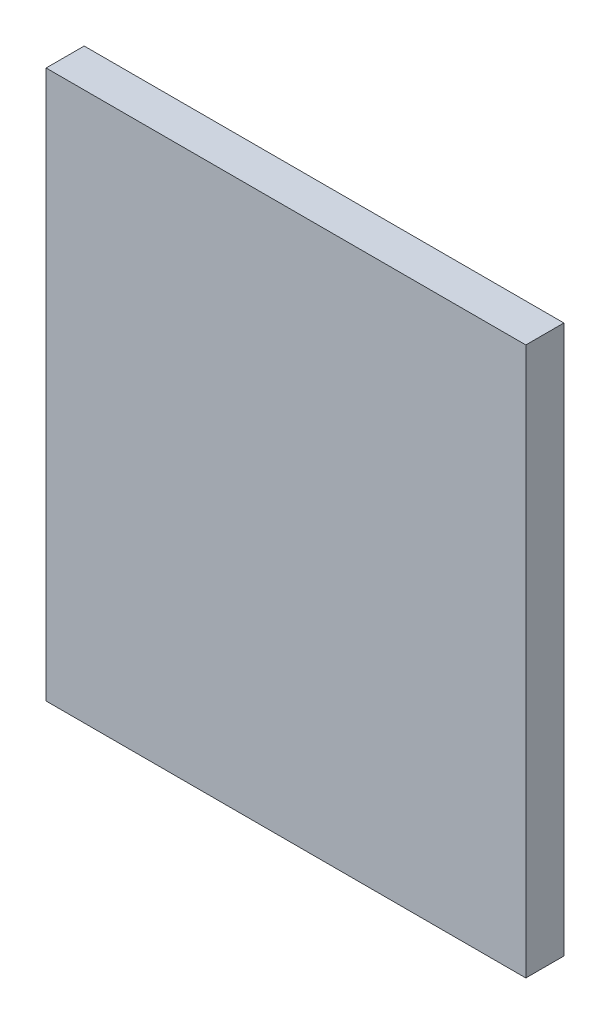
SolidWorks part; units mm, degrees
ref_plane "Front Plane" through (0, 0, 0) normal (0, 0, 1) x (1, 0, 0)
ref_plane "Top Plane" through (0, 0, 0) normal (0, 1, 0) x (1, 0, 0)
ref_plane "Right Plane" through (0, 0, 0) normal (1, 0, 0) x (0, 0, -1)
sketch "Sketch2" [suppressed] plane through (0, 0, 0) normal (0, 0, 1) x (1, 0, 0)
  line L0 (9.8069, 1.0971) -> (9.8069, -3.1704) construction
  line L1 (6.8551, -5.1618) -> (6.8551, -16.1618) construction
  line L2 (6.8551, -16.1618) -> (16.3814, -10.6618) construction
  line L3 (16.3814, -10.6618) -> (6.8551, -5.1618) construction
  line L4 (6.8551, -10.6618) -> (2.6647, -10.6618) construction
  line L5 (9.5069, 1.0971) -> (9.5069, -2.443)
  line L6 (6.5551, -6.3743) -> (6.5551, -9.8618)
  line L7 (8.0551, -15.8154) -> (15.4814, -11.5279)
  line L8 (15.4814, -9.7958) -> (8.0551, -5.5082)
  line L9 (6.0551, -10.3618) -> (3.5127, -10.3618)
  line L10 (10.1069, 1.0971) -> (10.1069, -2.3736)
  line L11 (7.1551, -6.5475) -> (7.1551, -14.7762)
  line L12 (7.9051, -15.2092) -> (15.0314, -11.0948)
  line L13 (15.0314, -10.2288) -> (7.9051, -6.1145)
  line L14 (6.0551, -10.9618) -> (3.5127, -10.9618)
  line L15 (9.5069, 1.0971) -> (9.5069, -3.1704) construction
  line L16 (10.1069, 1.0971) -> (10.1069, -3.1704) construction
  line L17 (6.8551, -10.9618) -> (2.6647, -10.9618) construction
  line L18 (6.8551, -10.3618) -> (2.6647, -10.3618) construction
  line L19 (6.5551, -11.4618) -> (6.5551, -14.9494)
  line L20 (6.5551, -4.6422) -> (6.5551, -16.6814) construction
  line L21 (7.1551, -15.6422) -> (15.7814, -10.6618) construction
  line L22 (15.7814, -10.6618) -> (7.1551, -5.6814) construction
  line L23 (7.1551, -5.6814) -> (7.1551, -15.6422) construction
  line L24 (6.5551, -16.6814) -> (16.9814, -10.6618) construction
  line L25 (16.9814, -10.6618) -> (6.5551, -4.6422) construction
  circle A0 centre (10.1647, -10.6618) radius 7.5 construction
  arc A1 (9.0767, -2.9381) -> (10.5803, -2.8729) centre (10.1647, -10.6618) ccw
  arc A2 (3.0162, -11.5215) -> (3.0162, -9.8021) centre (10.1647, -10.6618) ccw
  arc A3 (9.5069, 1.0971) -> (10.1069, 1.0971) centre (9.8069, 1.0971) cw
  circle A7 centre (10.1647, -10.6618) radius 7.8 construction
  circle A8 centre (10.1647, -10.6618) radius 7.2 construction
  arc A9 (10.1069, -2.3736) -> (10.5803, -2.8729) centre (10.6069, -2.3736) ccw
  arc A10 (9.5069, -2.443) -> (9.0767, -2.9381) centre (9.0069, -2.443) cw
  arc A11 (3.5127, -10.3618) -> (3.0162, -9.8021) centre (3.5127, -9.8618) cw
  arc A12 (3.5127, -10.9618) -> (3.0162, -11.5215) centre (3.5127, -11.4618) ccw
  arc A13 (6.0551, -10.3618) -> (6.5551, -9.8618) centre (6.0551, -9.8618) ccw
  arc A14 (6.5551, -11.4618) -> (6.0551, -10.9618) centre (6.0551, -11.4618) ccw
  arc A15 (15.0314, -11.0948) -> (15.0314, -10.2288) centre (14.7814, -10.6618) ccw
  arc A16 (7.1551, -14.7762) -> (7.9051, -15.2092) centre (7.6551, -14.7762) ccw
  arc A17 (7.1551, -6.5475) -> (7.9051, -6.1145) centre (7.6551, -6.5475) cw
  arc A18 (15.4814, -11.5279) -> (15.4814, -9.7958) centre (14.9814, -10.6618) ccw
  arc A19 (6.5551, -14.9494) -> (8.0551, -15.8154) centre (7.5551, -14.9494) ccw
  arc A20 (6.5551, -6.3743) -> (8.0551, -5.5082) centre (7.5551, -6.3743) cw
  point P1 (0, 0)
  point P9 (0, 0)
  point P10 (0, 0)
  point P11 (-3.6909, -2.988)
  point P12 (6.8551, -10.6618)
  point P13 (-4.1255, -2.8709)
  point P14 (5.6701, -7.3509)
  point P15 (-1.4676, -0.9486)
  point P18 (-9.5501, -9.1992)
  point P72 (0, 0)
  point P73 (0, 0)
  point P74 (0, -9.8504)
  point P75 (0, 0)
  point P76 (0, 0)
  dimension "D2" = 15
  dimension "D3" = 0.5
  dimension "D4" = 1
  dimension "D1" = 11
sketch "Sketch5" plane through (0, 0, 0) normal (0, 0, 1) x (1, 0, 0)
  line L1 (-31.5, 42) -> (31.5, 42)
  line L2 (-31.5, 42) -> (-31.5, -30)
  line L3 (-31.5, -30) -> (31.5, -30)
  line L4 (31.5, 42) -> (31.5, -30)
  point P4 (0, 42)
  dimension "D1" = 63
  dimension "D2" = 30
  dimension "D3" = 42
extrude "Boss-Extrude2" add sketch "Sketch5" along normal blind 5
sketch "Sketch1" plane through (0, 0, 5) normal (0, 0, 1) x (1, 0, 0)
  line L1 (-31, 17.6) -> (31, 17.6) construction
  line L2 (-31, 17.6) -> (-31, 0) construction
  line L3 (-31, 0) -> (31, 0) construction
  line L4 (31, 17.6) -> (31, 0) construction
  line L5 (-9.1, 38.0196) -> (9.1, 38.0196) construction
  line L6 (-9.1, 38.0196) -> (-9.1, 20.6196) construction
  line L7 (-9.1, 20.6196) -> (9.1, 20.6196) construction
  line L8 (9.1, 38.0196) -> (9.1, 20.6196) construction
  line L9 (-30.1379, -1.3413) -> (-1.1379, -1.3413) construction
  line L10 (-30.1379, -1.3413) -> (-30.1379, -28.8413) construction
  line L11 (-30.1379, -28.8413) -> (-1.1379, -28.8413) construction
  line L12 (-1.1379, -1.3413) -> (-1.1379, -28.8413) construction
  line L13 (-27.6379, -7.8413) -> (-3.6379, -7.8413) construction
  line L14 (-27.6379, -7.8413) -> (-27.6379, -22.8413) construction
  line L15 (-27.6379, -22.8413) -> (-3.6379, -22.8413) construction
  line L16 (-3.6379, -7.8413) -> (-3.6379, -22.8413) construction
  line L17 (0, 37.0153) -> (0, 31.2479) construction
  point P4 (0, 17.6)
  point P18 (0, 0)
  point P20 (-26.7166, -26.6413)
  point P21 (-3.2166, -26.6413)
  point P22 (-3.2166, -4.0013)
  point P23 (-26.7166, -3.1413)
  point P26 (6.1, 23.6196)
  point P27 (0, 38.0196)
  point P30 (-6.1, 23.6196)
  point P31 (0, 0)
  point P32 (-15.6379, -7.8413)
  point P33 (-15.6379, -28.8413)
  point P34 (-19.2322, 31.2479)
  point P35 (-19.5149, 37.0153)
  point P36 (0.3368, 64.9807)
  point P37 (-6.7789, 35.0196)
  point P38 (-6.7789, 24.0643)
  dimension "D1" = 17.6
  dimension "D2" = 18.2
  dimension "D3" = 17.4
  dimension "D4" = 27.5
  dimension "D5" = 29
  dimension "D6" = 15
  dimension "D7" = 24
  dimension "D8" = 6
  dimension "D9" = 23.5
  dimension "D10" = 23.5
  dimension "D11" = 12.2
  dimension "D12" = 3
  dimension "D13" = 62
  dimension "D14" = 1.8
sketch "Pause" plane through (0, 0, 5) normal (0, 0, 1) x (1, 0, 0)
  line L0 (12.2063, -1.8962) -> (12.2063, -9.8617) construction
  line L1 (13.3083, -11.763) -> (13.3083, -20.763) construction
  line L2 (19.3083, -11.763) -> (19.3083, -20.763) construction
  line L3 (8.6143, -16.263) -> (13.3083, -16.263) construction
  line L4 (19.3083, -16.263) -> (23.6143, -16.263) construction
  line L5 (13.3083, -11.763) -> (15.3083, -11.763) construction
  line L6 (15.3083, -11.763) -> (15.3083, -20.763) construction
  line L7 (15.3083, -20.763) -> (13.3083, -20.763) construction
  line L8 (19.3083, -11.763) -> (17.3083, -11.763) construction
  line L9 (17.3083, -11.763) -> (17.3083, -20.763) construction
  line L10 (17.3083, -20.763) -> (19.3083, -20.763) construction
  line L11 (11.9063, -1.8962) -> (11.9063, -9.4275)
  line L12 (13.0083, -12.163) -> (13.0083, -15.463)
  line L13 (14.9083, -21.063) -> (13.7083, -21.063)
  line L14 (15.6083, -12.163) -> (15.6083, -20.363)
  line L15 (13.7083, -11.463) -> (14.9083, -11.463)
  line L16 (19.6083, -12.163) -> (19.6083, -15.463)
  line L17 (17.7083, -21.063) -> (18.9083, -21.063)
  line L18 (17.0083, -12.163) -> (17.0083, -20.363)
  line L19 (18.9083, -11.463) -> (17.7083, -11.463)
  line L20 (8.6143, -16.563) -> (8.6203, -16.563)
  line L21 (20.1083, -16.563) -> (22.7664, -16.563)
  line L22 (12.5063, -1.8962) -> (12.5063, -8.5669)
  line L23 (13.6083, -12.563) -> (13.6083, -19.963)
  line L24 (14.5083, -20.463) -> (14.1083, -20.463)
  line L25 (15.0083, -12.563) -> (15.0083, -19.963)
  line L26 (14.1083, -12.063) -> (14.5083, -12.063)
  line L27 (19.0083, -12.563) -> (19.0083, -19.963)
  line L28 (18.1083, -20.463) -> (18.5083, -20.463)
  line L29 (17.6083, -12.563) -> (17.6083, -19.963)
  line L30 (18.5083, -12.063) -> (18.1083, -12.063)
  line L31 (8.6143, -15.963) -> (8.6203, -15.963)
  line L32 (20.1083, -15.963) -> (22.7664, -15.963)
  line L33 (11.9063, -1.8962) -> (11.9063, -9.8617) construction
  line L34 (9.4623, -16.563) -> (12.5083, -16.563)
  line L35 (12.5063, -1.8962) -> (12.5063, -9.8617) construction
  line L36 (8.6143, -16.563) -> (13.3083, -16.563) construction
  line L37 (9.4623, -15.963) -> (12.5083, -15.963)
  line L38 (8.6143, -15.963) -> (13.3083, -15.963) construction
  line L39 (13.0083, -17.063) -> (13.0083, -20.363)
  line L40 (13.0083, -11.463) -> (13.0083, -21.063) construction
  line L41 (19.3083, -15.963) -> (23.6143, -15.963) construction
  line L42 (19.6083, -17.063) -> (19.6083, -20.363)
  line L43 (19.6083, -11.463) -> (19.6083, -21.063) construction
  line L44 (19.3083, -16.563) -> (23.6143, -16.563) construction
  line L45 (23.6083, -15.963) -> (23.6143, -15.963)
  line L46 (23.6083, -16.563) -> (23.6143, -16.563)
  line L47 (17.6083, -20.463) -> (19.0083, -20.463) construction
  line L48 (17.6083, -12.063) -> (17.6083, -20.463) construction
  line L49 (19.0083, -12.063) -> (19.0083, -20.463) construction
  line L50 (19.0083, -12.063) -> (17.6083, -12.063) construction
  line L51 (13.6083, -12.063) -> (13.6083, -20.463) construction
  line L52 (15.0083, -20.463) -> (13.6083, -20.463) construction
  line L53 (15.0083, -12.063) -> (15.0083, -20.463) construction
  line L54 (13.6083, -12.063) -> (15.0083, -12.063) construction
  line L55 (17.0083, -11.463) -> (17.0083, -21.063) construction
  line L56 (19.6083, -11.463) -> (17.0083, -11.463) construction
  line L57 (17.0083, -21.063) -> (19.6083, -21.063) construction
  line L58 (15.6083, -21.063) -> (13.0083, -21.063) construction
  line L59 (15.6083, -11.463) -> (15.6083, -21.063) construction
  line L60 (13.0083, -11.463) -> (15.6083, -11.463) construction
  line L61 (12.2063, -1.8962) -> (12.2063, -9.8617) construction
  circle A0 centre (16.1143, -16.263) radius 7.5 construction
  arc A2 (11.69, -9.8393) -> (13.1936, -9.0305) centre (16.1143, -16.263) ccw
  arc A3 (8.9658, -17.1227) -> (23.2628, -17.1227) centre (16.1143, -16.263) ccw
  circle A4 centre (16.1143, -16.263) radius 7.8 construction
  circle A5 centre (16.1143, -16.263) radius 7.2 construction
  arc A6 (23.2628, -15.4033) -> (8.9658, -15.4033) centre (16.1143, -16.263) ccw
  arc A7 (11.9063, -9.4275) -> (11.69, -9.8393) centre (11.4063, -9.4275) cw
  arc A8 (13.1936, -9.0305) -> (12.5063, -8.5669) centre (13.0063, -8.5669) cw
  arc A9 (9.4623, -16.563) -> (8.9658, -17.1227) centre (9.4623, -17.063) ccw
  arc A10 (9.4623, -15.963) -> (8.9658, -15.4033) centre (9.4623, -15.463) cw
  arc A11 (22.7664, -15.963) -> (23.2628, -15.4033) centre (22.7664, -15.463) ccw
  arc A12 (23.2628, -17.1227) -> (22.7664, -16.563) centre (22.7664, -17.063) ccw
  arc A13 (20.1083, -15.963) -> (19.6083, -15.463) centre (20.1083, -15.463) cw
  arc A14 (20.1083, -16.563) -> (19.6083, -17.063) centre (20.1083, -17.063) ccw
  arc A15 (13.0083, -17.063) -> (12.5083, -16.563) centre (12.5083, -17.063) ccw
  arc A16 (12.5083, -15.963) -> (13.0083, -15.463) centre (12.5083, -15.463) ccw
  arc A17 (18.1083, -20.463) -> (17.6083, -19.963) centre (18.1083, -19.963) cw
  arc A18 (19.0083, -19.963) -> (18.5083, -20.463) centre (18.5083, -19.963) cw
  arc A19 (19.0083, -12.563) -> (18.5083, -12.063) centre (18.5083, -12.563) ccw
  arc A20 (17.6083, -12.563) -> (18.1083, -12.063) centre (18.1083, -12.563) cw
  arc A21 (13.6083, -19.963) -> (14.1083, -20.463) centre (14.1083, -19.963) ccw
  arc A22 (14.5083, -20.463) -> (15.0083, -19.963) centre (14.5083, -19.963) ccw
  arc A23 (15.0083, -12.563) -> (14.5083, -12.063) centre (14.5083, -12.563) ccw
  arc A24 (13.6083, -12.563) -> (14.1083, -12.063) centre (14.1083, -12.563) cw
  arc A25 (17.0083, -12.163) -> (17.7083, -11.463) centre (17.7083, -12.163) cw
  arc A26 (19.6083, -12.163) -> (18.9083, -11.463) centre (18.9083, -12.163) ccw
  arc A27 (19.6083, -20.363) -> (18.9083, -21.063) centre (18.9083, -20.363) cw
  arc A28 (17.7083, -21.063) -> (17.0083, -20.363) centre (17.7083, -20.363) cw
  arc A29 (13.0083, -20.363) -> (13.7083, -21.063) centre (13.7083, -20.363) ccw
  arc A30 (14.9083, -21.063) -> (15.6083, -20.363) centre (14.9083, -20.363) ccw
  arc A31 (15.6083, -12.163) -> (14.9083, -11.463) centre (14.9083, -12.163) ccw
  arc A32 (13.0083, -12.163) -> (13.7083, -11.463) centre (13.7083, -12.163) cw
  point P18 (13.3083, -16.263)
  point P73 (23.3081, -15.963)
  point P132 (12.1872, -1.5141)
  point P134 (0, 0)
  point P135 (12.2063, -1.8962)
  dimension "D5" = 15
  dimension "D6" = 0.5
  dimension "D7" = 0.7
  dimension "D1" = 2
  dimension "D2" = 2
  dimension "D3" = 2
  dimension "D4" = 9
